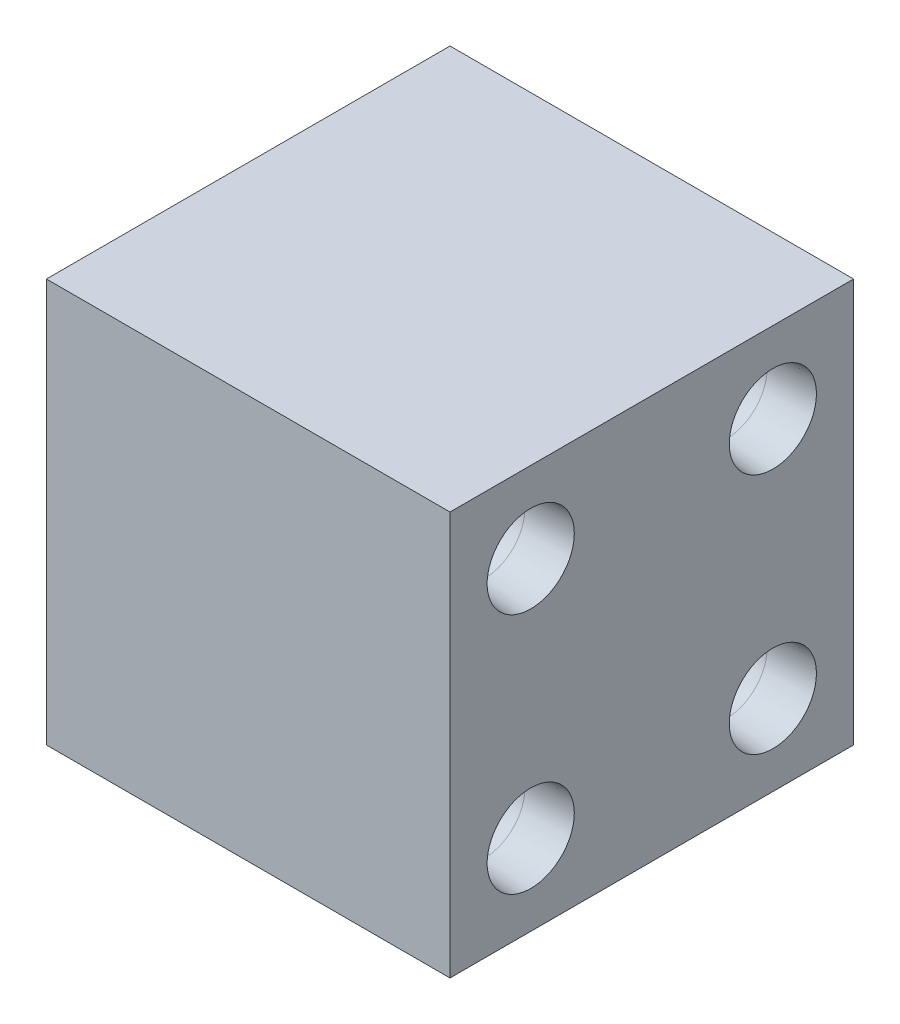
SolidWorks part; units mm, degrees
ref_plane "Front Plane" through (0, 0, 0) normal (0, 0, 1) x (1, 0, 0)
ref_plane "Top Plane" through (0, 0, 0) normal (0, 1, 0) x (1, 0, 0)
ref_plane "Right Plane" through (0, 0, 0) normal (1, 0, 0) x (0, 0, -1)
sketch "Sketch2" plane through (0, 0, 0) normal (0, 1, 0) x (1, 0, 0)
  line L1 (-12.5, 12.5) -> (12.5, 12.5)
  line L2 (-12.5, 12.5) -> (-12.5, -12.5)
  line L3 (-12.5, -12.5) -> (12.5, -12.5)
  line L4 (12.5, 12.5) -> (12.5, -12.5)
  line L5 (-12.5, 12.5) -> (12.5, -12.5) construction
  line L6 (-12.5, -12.5) -> (12.5, 12.5) construction
  point P0 (0, 0)
  dimension "D1" = 25
  dimension "D2" = 25
extrude "Boss-Extrude1" add sketch "Sketch2" along normal blind 25
hole_wizard "CSK for M3 Oval Head Machine Screw1" positions "Sketch3" profile "Sketch4" countersink size "M3" standard "ANSI Metric"
sketch "Sketch3" plane through (-12.5, 0, 0) normal (-1, 0, 0) x (0, 0, 1)
  line L0 (-12.5, 25) -> (12.5, 25) construction
  line L1 (-12.5, 25) -> (-12.5, 0) construction
  point P0 (-7.5, 20)
  dimension "D1" = 5
  dimension "D2" = 5
sketch "Sketch4" plane through (-12.5, 20, -7.5) normal (0, 1, 0) x (0, 0, 1)
  line L0 (0, 0) -> (0, 11.5022)
  line L1 (0, 11.5022) -> (2.5, 10)
  line L2 (2.5, 10) -> (2.5, 2.8601)
  line L3 (2.5, 2.8601) -> (2.7, 0)
  line L5 (2.7, 0) -> (0, 0)
  line L6 (-2.5, 2.8601) -> (-2.7, 0) construction
  line L10 (0, 11.5022) -> (-2.5, 10) construction
  line L11 (0, -6.35) -> (0, 107.95) construction
  dimension "Hole Dia." = 5
  dimension "Hole Depth" = 10
  dimension "Near C'Sink Dia." = 5.4
  dimension "Near C'Sink Angle" = 8
  dimension "Drill Angle" = 118
pattern_linear "LPattern1" count 2 spacing 15 along (0, -1, 0) count 2 spacing 15 along (0, 0, 1) of "CSK for M3 Oval Head Machine Screw1"
mirror "Mirror1" about plane through (0, 0, 0) normal (1, 0, 0) of "LPattern1", "CSK for M3 Oval Head Machine Screw1"
